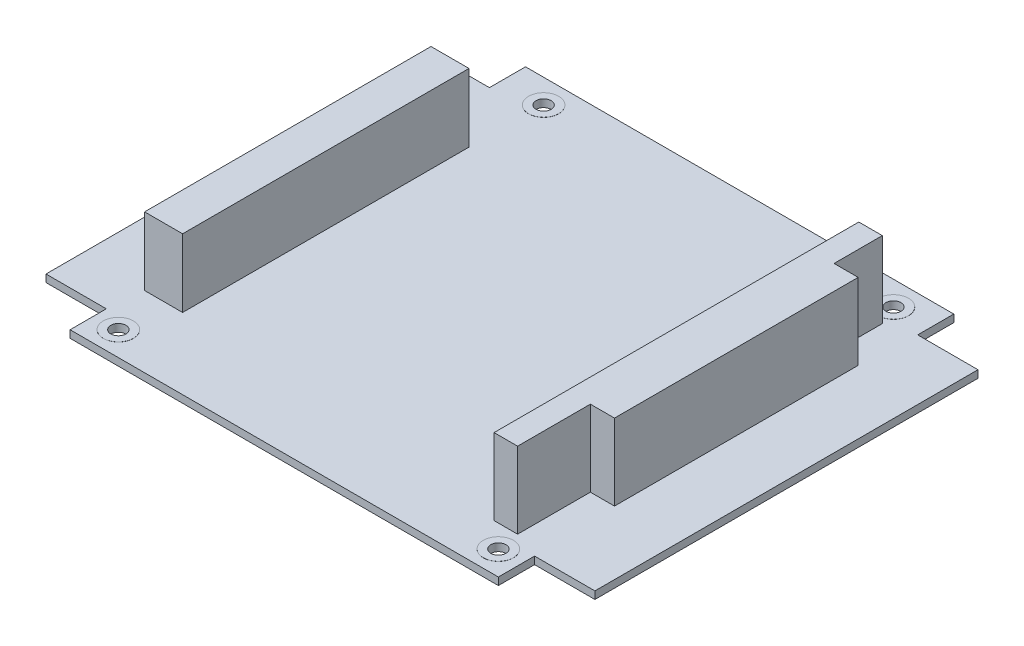
SolidWorks part; units mm, degrees
ref_plane "Plane1" through (0, 0, 0) normal (0, 0, 1) x (1, 0, 0)
ref_plane "Plane2" through (0, 0, 0) normal (0, 1, 0) x (1, 0, 0)
ref_plane "Plane3" through (0, 0, 0) normal (1, 0, 0) x (0, 0, -1)
sketch "Sketch1" plane through (0, 0, 0) normal (0, 1, 0) x (1, 0, 0)
  line L0 (-45.085, 47.945) -> (45.085, -47.945) construction
  line L1 (-45.085, 47.945) -> (45.085, 47.945)
  line L2 (-45.085, 47.945) -> (-45.085, 40.3434)
  line L3 (-45.085, -47.945) -> (45.085, -47.945)
  line L4 (45.085, 47.945) -> (45.085, 40.3434)
  line L5 (45.085, 40.3434) -> (57.785, 40.3434)
  line L6 (57.785, 40.3434) -> (57.785, -40.3181)
  line L7 (-57.785, 0.0126) -> (57.785, 0.0126) construction
  line L8 (0, 47.945) -> (0, -47.945) construction
  line L9 (45.085, -40.3181) -> (57.785, -40.3181)
  line L10 (-45.085, -40.3181) -> (-57.785, -40.3181)
  line L11 (-57.785, 40.3434) -> (-57.785, -40.3181)
  line L12 (-45.085, 40.3434) -> (-57.785, 40.3434)
  line L13 (45.085, -40.3181) -> (45.085, -47.945)
  line L14 (-45.085, -40.3181) -> (-45.085, -47.945)
  point P14 (57.785, 0.0126)
  point P18 (-57.785, 0.0126)
  dimension "D1" = 95.89
  dimension "D2" = 90.17
  dimension "D3" = 12.7
extrude "Base-Extrude" add sketch "Sketch1" along normal blind 1.57
sketch "Sketch2" plane through (0, 1.57, 0) normal (0, 1, 0) x (-1, 0, 0)
  line L1 (45.085, 47.945) -> (-45.085, 47.945) construction
  line L2 (-45.085, 47.945) -> (-45.085, 40.3181) construction
  line L3 (45.085, 47.945) -> (-45.085, 47.945) construction
  line L4 (45.085, 40.3181) -> (45.085, 47.945) construction
  line L6 (45.085, -47.945) -> (45.085, -40.3434) construction
  circle A0 centre (36.195, -42.865) radius 1.59
  circle A1 centre (40.005, 42.865) radius 1.59
  circle A2 centre (-40.005, 42.865) radius 1.59
  circle A3 centre (-37.465, -42.865) radius 1.59
  dimension "D7" = 3.18
  dimension "D5" = 90.81
  dimension "D8" = 8.89
  dimension "D9" = 82.55
  dimension "D1" = 5.08
  dimension "D2" = 5.08
  dimension "D3" = 5.08
  dimension "D4" = 5.08
  dimension "D6" = 90.81
extrude "Mounting Holes" cut sketch "Sketch2" against normal through all
sketch "Sketch3" plane through (0, 1.57, 0) normal (0, 1, 0) x (-1, 0, 0)
  circle A0 centre (36.195, -42.865) radius 3.175
  circle A1 centre (-37.465, -42.865) radius 3.175
  circle A2 centre (-40.005, 42.865) radius 3.175
  circle A3 centre (40.005, 42.865) radius 3.175
  circle A4 centre (40.005, 42.865) radius 1.59 construction
  circle A5 centre (36.195, -42.865) radius 1.59 construction
  circle A6 centre (-37.465, -42.865) radius 1.59 construction
  circle A7 centre (-40.005, 42.865) radius 1.59 construction
  circle A8 centre (40.005, 42.865) radius 1.59
  circle A9 centre (-40.005, 42.865) radius 1.59
  circle A10 centre (-37.465, -42.865) radius 1.59
  circle A11 centre (36.195, -42.865) radius 1.59
  dimension "D1" = 6.35
extrude "Top Pads" add sketch "Sketch3" along normal blind 0.02
sketch "Sketch4" plane through (0, 0, 0) normal (0, -1, 0) x (1, 0, 0)
  circle A8 centre (-36.195, -42.865) radius 1.59 construction
  circle A9 centre (-36.195, -42.865) radius 3.175 construction
  circle A10 centre (37.465, -42.865) radius 1.59 construction
  circle A11 centre (37.465, -42.865) radius 3.175 construction
  circle A12 centre (40.005, 42.865) radius 1.59 construction
  circle A13 centre (40.005, 42.865) radius 3.175 construction
  circle A14 centre (-40.005, 42.865) radius 1.59 construction
  circle A15 centre (-40.005, 42.865) radius 3.175 construction
  circle A16 centre (-36.195, -42.865) radius 1.59
  circle A17 centre (-36.195, -42.865) radius 3.175
  circle A18 centre (37.465, -42.865) radius 1.59
  circle A19 centre (37.465, -42.865) radius 3.175
  circle A20 centre (40.005, 42.865) radius 1.59
  circle A21 centre (40.005, 42.865) radius 3.175
  circle A22 centre (-40.005, 42.865) radius 1.59
  circle A23 centre (-40.005, 42.865) radius 3.175
extrude "Bott Pads" add sketch "Sketch4" along normal blind 0.02
sketch "Sketch5" plane through (0, 1.57, 0) normal (0, 1, 0) x (-1, 0, 0)
  line L0 (-39.305, 22.795) -> (-39.305, 38.115)
  line L1 (-34.355, -38.675) -> (-39.305, -38.675)
  line L2 (-34.355, -38.675) -> (-34.355, 38.115)
  line L3 (-34.355, 38.115) -> (-39.305, 38.115)
  line L4 (-39.305, -38.675) -> (-39.305, -28.515)
  line L5 (-39.305, -28.515) -> (-44.385, -28.515)
  line L6 (45.085, 47.945) -> (-45.085, 47.945) construction
  line L7 (-39.305, 22.795) -> (-44.385, 22.795)
  line L8 (-44.385, -28.515) -> (-44.385, 22.795)
  line L9 (-57.785, 40.3181) -> (-57.785, -40.3434) construction
  dimension "D1" = 15.32
  dimension "D2" = 66.63
  dimension "D3" = 76.79
  dimension "D4" = 10.03
  dimension "D5" = 4.95
  dimension "D6" = 9.83
  dimension "D7" = 13.4
extrude "ISA Cnct" add sketch "Sketch5" along normal blind 16.05
sketch "Sketch6" plane through (0, 1.57, 0) normal (0, 1, 0) x (-1, 0, 0)
  line L0 (45.085, 47.945) -> (-45.085, 47.945) construction
  line L1 (44.385, -27.345) -> (36.385, -27.345)
  line L2 (44.385, -27.345) -> (44.385, 32.955)
  line L3 (44.385, 32.955) -> (36.385, 32.955)
  line L4 (36.385, -27.345) -> (36.385, 32.955)
  line L5 (-57.785, 40.3181) -> (-57.785, -40.3434) construction
  dimension "D1" = 14.99
  dimension "D2" = 102.17
  dimension "D3" = 8
  dimension "D4" = 60.3
extrude "PCI Cnct" add sketch "Sketch6" along normal blind 14.35
sketch "Sketch7" plane through (0, 0, 0) normal (0, -1, 0) x (1, 0, 0)
  line L0 (-44.385, 2.805) -> (-36.385, 2.805) construction
  line L1 (-46.035, 34.48) -> (-34.735, 34.48)
  line L2 (-46.035, 34.48) -> (-46.035, -28.87)
  line L3 (-46.035, -28.87) -> (-34.735, -28.87)
  line L4 (-34.735, 34.48) -> (-34.735, -28.87)
  line L5 (-44.64, 33.285) -> (-36.13, 33.285)
  line L6 (-44.64, 33.285) -> (-44.64, -27.675)
  line L7 (-44.64, -27.675) -> (-36.13, -27.675)
  line L8 (-36.13, 33.285) -> (-36.13, -27.675)
  line L9 (-44.385, -27.345) -> (-44.385, 32.955) construction
  line L10 (-36.385, -27.345) -> (-36.385, 32.955) construction
  line L11 (-40.385, 32.955) -> (-40.385, -27.345) construction
  line L12 (-44.385, 32.955) -> (-36.385, 32.955) construction
  line L13 (-44.385, -27.345) -> (-36.385, -27.345) construction
  point P8 (-40.385, 33.285)
  point P21 (-40.385, -27.675)
  point P22 (-44.64, 2.805)
  point P23 (-46.035, 2.805)
  point P24 (-40.385, 34.48)
  dimension "D1" = 63.35
  dimension "D2" = 11.3
  dimension "D3" = 8.51
  dimension "D4" = 60.96
extrude "PCI Cnct Shroud" [suppressed] add sketch "Sketch7" along normal blind 11.18
sketch "Sketch8" plane through (0, 0, 0) normal (0, -1, 0) x (1, 0, 0)
  line L1 (35.555, -36.835) -> (36.195, -36.835)
  line L2 (35.555, -36.835) -> (35.555, -37.475)
  line L3 (35.555, -37.475) -> (36.195, -37.475)
  line L4 (36.195, -36.835) -> (36.195, -37.475)
  line L5 (37.075, -36.835) -> (37.715, -36.835)
  line L6 (37.075, -36.835) -> (37.075, -37.475)
  line L7 (37.075, -37.475) -> (37.715, -37.475)
  line L8 (37.715, -36.835) -> (37.715, -37.475)
  line L9 (35.555, -37.155) -> (36.195, -37.155) construction
  line L10 (35.875, -36.835) -> (35.875, -37.475) construction
  line L11 (39.305, -38.675) -> (34.355, -38.675) construction
  line L12 (34.355, -38.675) -> (34.355, 38.115) construction
  line L13 (37.075, -37.155) -> (37.715, -37.155) construction
  line L14 (37.395, -36.835) -> (37.395, -37.475) construction
  point P12 (37.075, -37.155)
  dimension "D1" = 1.52
  dimension "D2" = 1.52
  dimension "D3" = 0.64
  dimension "D4" = 1.52
extrude "Bot ISA" [suppressed] add sketch "Sketch8" along normal blind 10.67
pattern_linear "LPattern1" [suppressed] count 32 spacing 2.54
sketch "Sketch9" [suppressed] plane through (0, 0, 0) normal (0, -1, 0) x (1, 0, 0)
  line L0 (37.715, -37.475) -> (37.715, -36.835) construction
  line L1 (40.005, -26.675) -> (40.645, -26.675)
  line L2 (40.005, -26.675) -> (40.005, -27.315)
  line L3 (40.005, -27.315) -> (40.645, -27.315)
  line L4 (40.645, -26.675) -> (40.645, -27.315)
  line L5 (42.545, -26.675) -> (43.185, -26.675)
  line L6 (42.545, -26.675) -> (42.545, -27.315)
  line L7 (42.545, -27.315) -> (43.185, -27.315)
  line L8 (43.185, -26.675) -> (43.185, -27.315)
  line L9 (44.385, -28.515) -> (39.305, -28.515) construction
  line L10 (42.545, -26.995) -> (43.185, -26.995) construction
  line L11 (40.005, -26.995) -> (40.645, -26.995) construction
  line L12 (40.325, -26.675) -> (40.325, -27.315) construction
  line L13 (42.865, -26.675) -> (42.865, -27.315) construction
  line L14 (44.385, 22.795) -> (44.385, -28.515) construction
  point P10 (42.865, -27.315)
  dimension "D1" = 1.52
  dimension "D2" = 2.54
  dimension "D3" = 1.52
extrude "Boss-Extrude7" [suppressed] add sketch "Sketch9" along normal up to surface (10.67 mm away)
pattern_linear "LPattern2" [suppressed] count 20 spacing 2.54
sketch "Sketch10" [suppressed] plane through (0, 0, 0) normal (0, -1, 0) x (1, 0, 0)
  line L0 (-43.395, -25.925) -> (-43.395, -25.425) construction
  line L1 (-43.645, -25.925) -> (-43.145, -25.925)
  line L2 (-43.645, -25.925) -> (-43.645, -25.425)
  line L3 (-43.645, -25.425) -> (-43.145, -25.425)
  line L4 (-43.145, -25.925) -> (-43.145, -25.425)
  line L5 (-43.645, -25.675) -> (-43.145, -25.675) construction
  line L6 (-44.64, -27.675) -> (-36.13, -27.675) construction
  line L9 (-46.035, 34.48) -> (-46.035, -28.87) construction
  dimension "D1" = 2
  dimension "D2" = 2.64
  dimension "D3" = 0.5
extrude "PCI Base" [suppressed] add sketch "Sketch10" along normal blind 10.41
pattern_linear "LPattern3" [suppressed] count 30 spacing 2
pattern_linear "LPattern4" [suppressed] count 4 spacing 2
